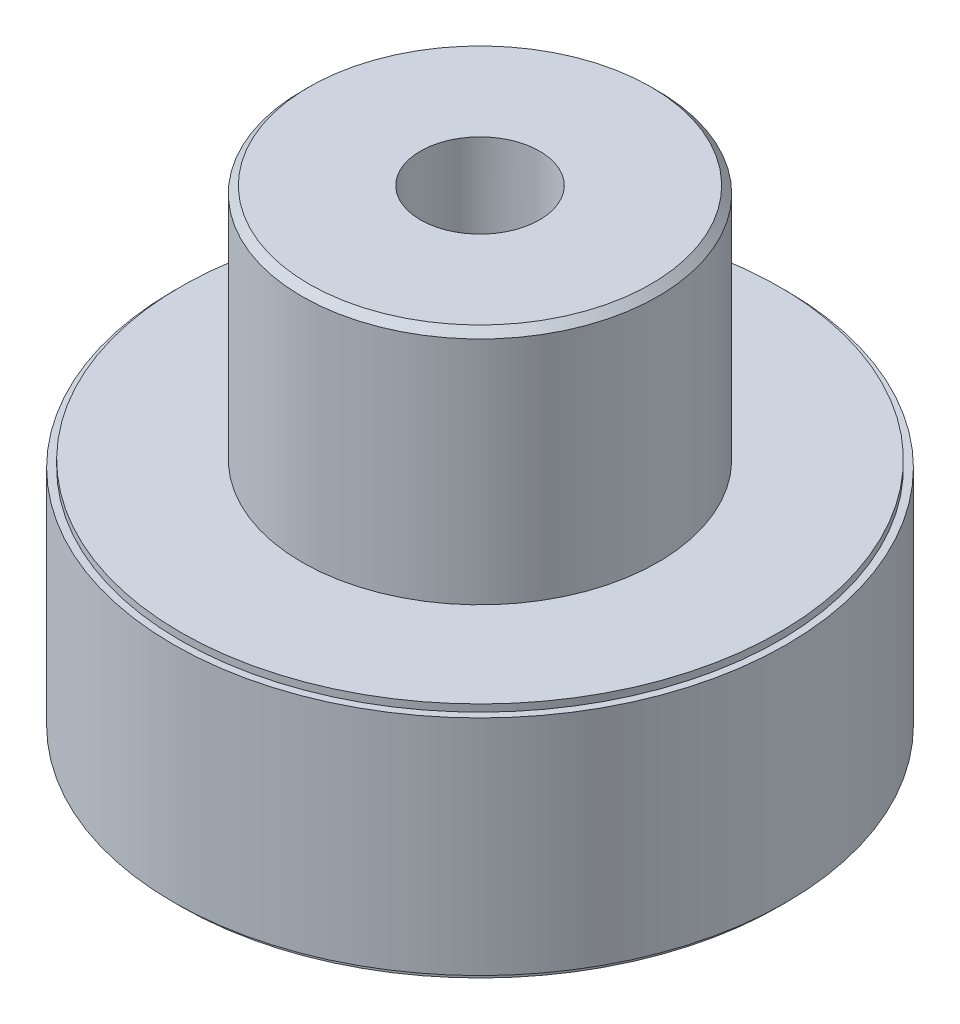
SolidWorks part; units mm, degrees
ref_plane "Front Plane" through (0, 0, 0) normal (0, 0, 1) x (1, 0, 0)
ref_plane "Top Plane" through (0, 0, 0) normal (0, 1, 0) x (1, 0, 0)
ref_plane "Right Plane" through (0, 0, 0) normal (1, 0, 0) x (0, 0, -1)
sketch "Sketch1" plane through (0, 0, 0) normal (0, 1, 0) x (1, 0, 0)
  circle A0 centre (0, 0) radius 16.02
extrude "Boss-Extrude1" add sketch "Sketch1" along normal blind 0.38
sketch "Sketch2" plane through (0, 0.38, 0) normal (0, 1, 0) x (1, 0, 0)
  circle A0 centre (0, 0) radius 16.4
extrude "Boss-Extrude2" add sketch "Sketch2" along normal blind 11.94
sketch "Sketch3" plane through (0, 12.32, 0) normal (0, 1, 0) x (1, 0, 0)
  circle A0 centre (0, 0) radius 16.02
extrude "Boss-Extrude3" add sketch "Sketch3" along normal blind 0.38
sketch "Sketch4" plane through (0, 12.7, 0) normal (0, 1, 0) x (1, 0, 0)
  circle A0 centre (0, 0) radius 9.525
extrude "Boss-Extrude4" add sketch "Sketch4" along normal blind 12.32
sketch "Sketch5" plane through (0, 25.02, 0) normal (0, 1, 0) x (1, 0, 0)
  circle A0 centre (0, 0) radius 9.525
extrude "Boss-Extrude5" add sketch "Sketch5" along normal blind 0.38 draft 45
sketch "Sketch6" plane through (0, 25.4, 0) normal (0, 1, 0) x (1, 0, 0)
  circle A0 centre (0, 0) radius 3.19
extrude "Cut-Extrude1" cut sketch "Sketch6" against normal blind 19.05
sketch "Sketch7" plane through (0, 6.35, 0) normal (0, 1, 0) x (1, 0, 0)
  circle A0 centre (0, 0) radius 12.32
extrude "Cut-Extrude5" cut sketch "Sketch7" against normal blind 0.38 draft 45 draft outward yes
sketch "Sketch11" plane through (0, 5.97, 0) normal (0, 1, 0) x (1, 0, 0)
  circle A0 centre (0, 0) radius 12.7
extrude "Cut-Extrude6" cut sketch "Sketch11" against normal blind 5.97
sketch "Sketch13" plane through (0, 0, 0) normal (0, 0, 1) x (1, 0, 0)
  circle A0 centre (0, 18.86) radius 2.02
  point P0 (0, 18.86)
extrude "Cut-Extrude7" cut sketch "Sketch13" against normal blind 10.97
